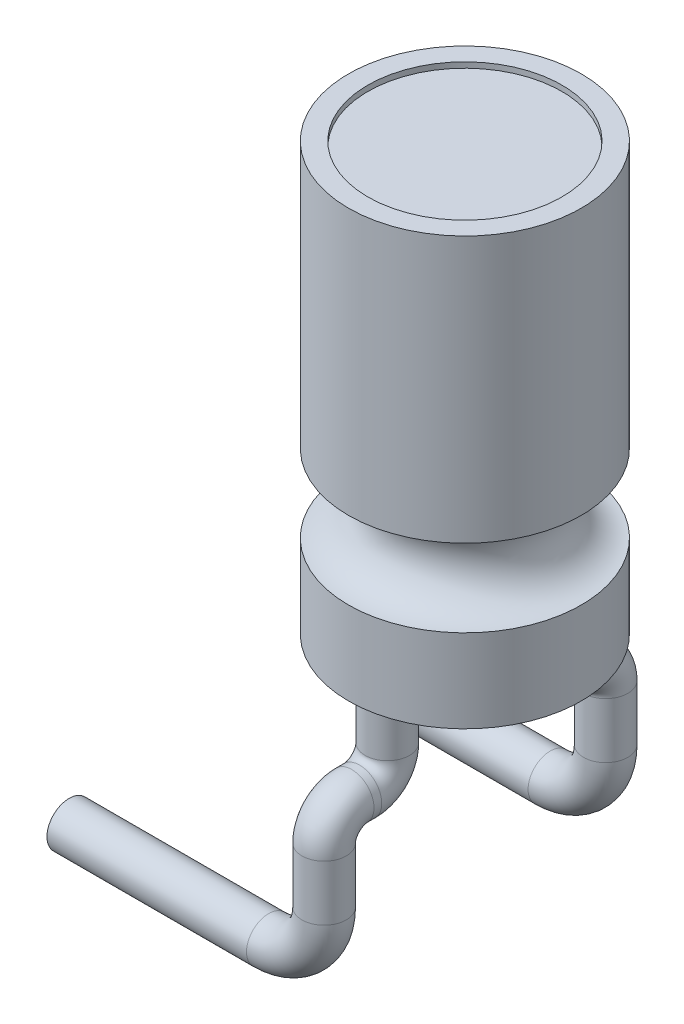
SolidWorks part; units mm, degrees
ref_plane "Face" through (0, 0, 0) normal (0, 0, 1) x (1, 0, 0)
ref_plane "Dessus" through (0, 0, 0) normal (0, 1, 0) x (1, 0, 0)
ref_plane "Droite" through (0, 0, 0) normal (1, 0, 0) x (0, 0, -1)
sketch "Esquisse1" plane through (0, 0, 0) normal (0, 0, 1) x (1, 0, 0)
  line L0 (0, 48.4017) -> (0, -33.7592) construction
  line L1 (0, 35.2164) -> (2.1, 35.2164)
  line L2 (2.1, 35.2164) -> (2.1, 30.4164)
  line L3 (2.1, 29.0164) -> (2.1, 27.5164)
  line L4 (2.1, 27.5164) -> (0, 27.5164)
  line L5 (0, 27.5164) -> (0, 35.2164)
  line L6 (9.8114, 29.7164) -> (-7.1309, 29.7164) construction
  line L7 (2.1, 25.0819) -> (2.1, 32.6721) construction
  line L8 (5.1241, 27.5164) -> (-5.6865, 27.5164) construction
  line L9 (5.1241, 29.0164) -> (-3.1767, 29.0164) construction
  arc A0 (2.1, 30.4164) -> (2.1, 29.0164) centre (2.1, 29.7164) ccw
  dimension "D4" = 0.7
  dimension "D1" = 7.7
  dimension "D2" = 2.1
  dimension "D3" = 1.5
revolve "Révolution1" add sketch "Esquisse1" angle 360 about L0
sketch "Esquisse2" plane through (0, 35.2164, 0) normal (0, 1, 0) x (-1, 0, 0)
  circle A0 centre (0, 0) radius 1.75
  dimension "D1" = 3.5
extrude "Enlèv. mat.-Extru.1" cut sketch "Esquisse2" against normal blind 0.1
sketch "Esquisse3" plane through (0, 27.5164, 0) normal (0, -1, 0) x (1, 0, 0)
  line L0 (4.0351, 0) -> (-4.283, 0) construction
  line L1 (0, 6.7464) -> (0, -6.9013) construction
  circle A0 centre (0, 1.4) radius 0.4
  dimension "D1" = 0.8
sketch "Esquisse4" plane through (0, 0, 0) normal (1, 0, 0) x (0, 0, -1)
  line L0 (-1.4, 24.8484) -> (-1.4, 29.3314) construction
  line L1 (-5.5325, 26.0164) -> (6.9013, 26.0164) construction
  line L2 (-2.54, 26.4376) -> (-2.54, 18.8472) construction
  line L3 (-8.7913, 27.5164) -> (10.5025, 27.5164) construction
  line L4 (0, 26.7733) -> (0, 22.2147) construction
  line L6 (-1.4, 27.5164) -> (-1.4, 26.5164)
  line L7 (-1.9, 26.0164) -> (-2.04, 26.0164)
  arc A0 (-1.4, 26.5164) -> (-1.9, 26.0164) centre (-1.9, 26.5164) cw
  arc A1 (-2.04, 26.0164) -> (-2.54, 25.5164) centre (-2.04, 25.5164) ccw
  dimension "D4" = 0.5
  dimension "D1" = 1.5
  dimension "D2" = 2.54
sweep "Balayage1" add profiles "Esquisse3" path "Esquisse4"
sketch "Esquisse5" plane through (0, 25.5164, 0) normal (0, -1, 0) x (1, 0, 0)
  line L0 (0, 2.8846) -> (0, 1.9) construction
  line L1 (0.1862, 2.54) -> (-0.4, 2.54) construction
  circle A0 centre (0, 2.54) radius 0.4
ref_plane "Plan1" through (0, 0, 2.54) normal (0, 0, 1) x (1, 0, 0)
sketch "Esquisse6" plane through (0, 0, 2.54) normal (0, 0, 1) x (1, 0, 0)
  line L0 (0, 25.7821) -> (0, 22.579) construction
  line L1 (1.0149, 23.5164) -> (-9.4986, 23.5164) construction
  line L2 (1.2934, 25.5164) -> (-9.4986, 25.5164) construction
  line L3 (-2.6, 27.2212) -> (-2.6, 21.8479) construction
  line L4 (-4.6, 21.8479) -> (-4.6, 27.2212) construction
  line L5 (0, 25.5164) -> (0, 24.5164)
  line L6 (-1, 23.5164) -> (-4.6, 23.5164)
  arc A0 (0, 24.5164) -> (-1, 23.5164) centre (-1, 24.5164) cw
  dimension "D3" = 1
  dimension "D1" = 2
  dimension "D2" = 2
sweep "Balayage2" add profiles "Esquisse5" path "Esquisse6"
ref_plane "Plan2" through (0, 0, 0) normal (0, 0, 1) x (1, 0, 0)
mirror "Symétrie1" about plane through (0, 0, 0) normal (0, 0, 1) of "Balayage2", "Balayage1"
